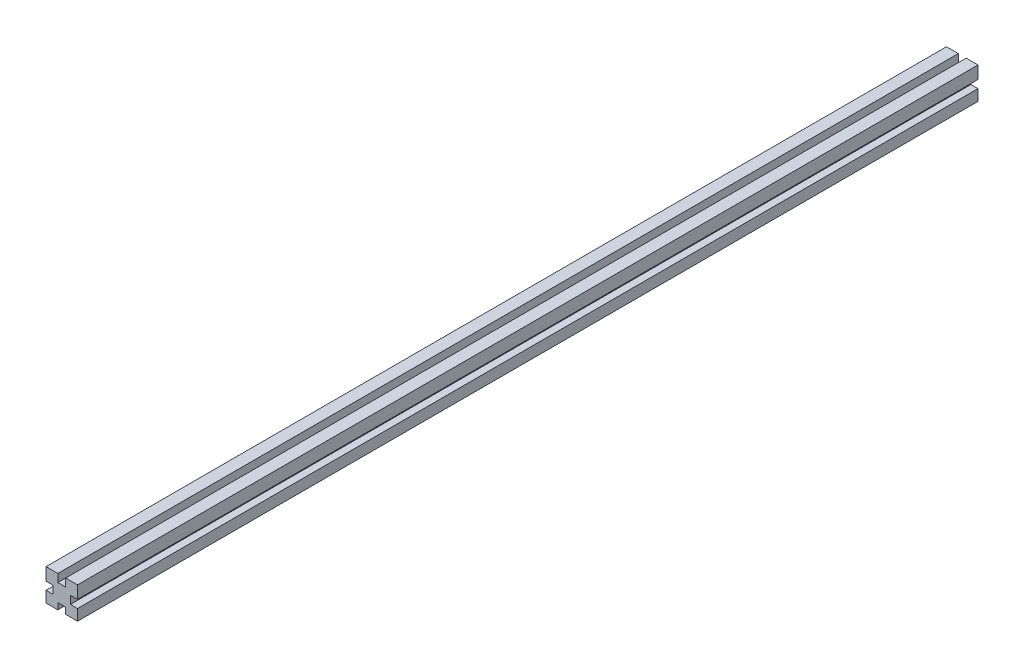
SolidWorks part; units mm, degrees
ref_plane "Front Plane" through (0, 0, 0) normal (0, 0, 1) x (1, 0, 0)
ref_plane "Top Plane" through (0, 0, 0) normal (0, 1, 0) x (1, 0, 0)
ref_plane "Right Plane" through (0, 0, 0) normal (1, 0, 0) x (0, 0, -1)
sketch "Sketch1" plane through (0, 0, 0) normal (0, 0, 1) x (1, 0, 0)
  line L1 (-10, 10) -> (10, 10)
  line L2 (-10, 10) -> (-10, -10)
  line L3 (-10, -10) -> (10, -10)
  line L4 (10, 10) -> (10, -10)
  line L5 (-10, 10) -> (10, -10) construction
  line L6 (-10, -10) -> (10, 10) construction
  point P0 (0, 0)
  dimension "D1" = 20
  dimension "D2" = 20
extrude "Boss-Extrude1" add sketch "Sketch1" against normal blind 571
sketch "Sketch2" plane through (0, 0, 0) normal (0, 0, 1) x (1, 0, 0)
  line L0 (10, 10) -> (-10, 10) construction
  line L1 (-2.5, 15) -> (2.5, 15)
  line L2 (-2.5, 15) -> (-2.5, 5)
  line L3 (-2.5, 5) -> (2.5, 5)
  line L4 (2.5, 15) -> (2.5, 5)
  line L5 (-2.5, 15) -> (2.5, 5) construction
  line L6 (-2.5, 5) -> (2.5, 15) construction
  point P0 (0, 10)
  dimension "D1" = 5
  dimension "D2" = 10
extrude "Cut-Extrude1" cut sketch "Sketch2" against normal through all
pattern_circular "CirPattern1" count 4 over 360 about axis through (0, -0.5, 0) along (0, 0, 1) of "Cut-Extrude1"
